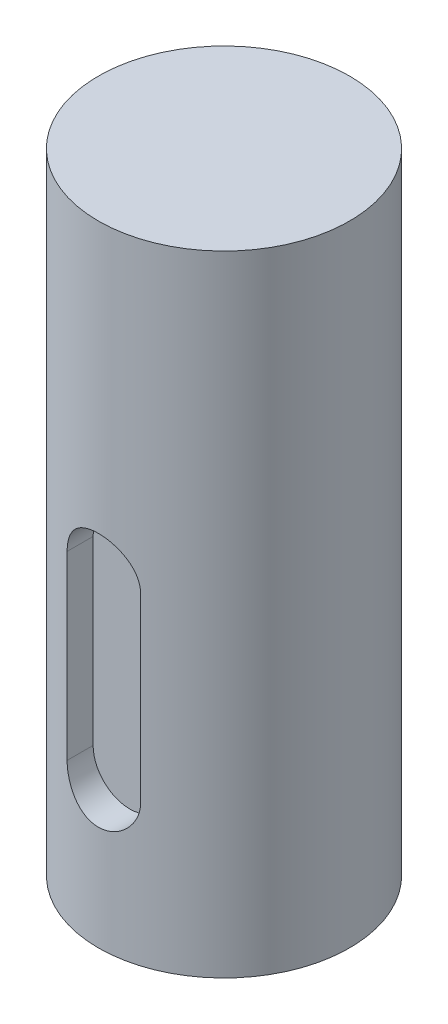
SolidWorks part; units mm, degrees
ref_plane "前视基准面" through (0, 0, 0) normal (0, 0, 1) x (1, 0, 0)
ref_plane "上视基准面" through (0, 0, 0) normal (0, 1, 0) x (1, 0, 0)
ref_plane "右视基准面" through (0, 0, 0) normal (1, 0, 0) x (0, 0, -1)
sketch "草图1" plane through (0, 0, 0) normal (0, 1, 0) x (1, 0, 0)
  circle A0 centre (0, 0) radius 19.9517
extrude "凸台-拉伸1" add sketch "草图1" along normal blind 100
ref_plane "基准面1" through (0, 0, 19.9517) normal (0, 0, 1) x (1, 0, 0)
sketch "草图2" plane through (0, 0, 19.9517) normal (0, 0, 1) x (1, 0, 0)
  line L0 (0, 22.4489) -> (0, 51.1979) construction
  line L1 (-5.8396, 22.4489) -> (-5.8396, 51.1979)
  line L2 (5.8396, 22.4489) -> (5.8396, 51.1979)
  arc A0 (-5.8396, 22.4489) -> (5.8396, 22.4489) centre (0, 22.4489) ccw
  arc A1 (5.8396, 51.1979) -> (-5.8396, 51.1979) centre (0, 51.1979) ccw
  point P3 (0, 36.8234)
extrude "切除-拉伸1" cut sketch "草图2" against normal blind 5
ref_plane "基准面2" through (-19.9517, 0, 0) normal (-1, 0, 0) x (0, 0, 1)
